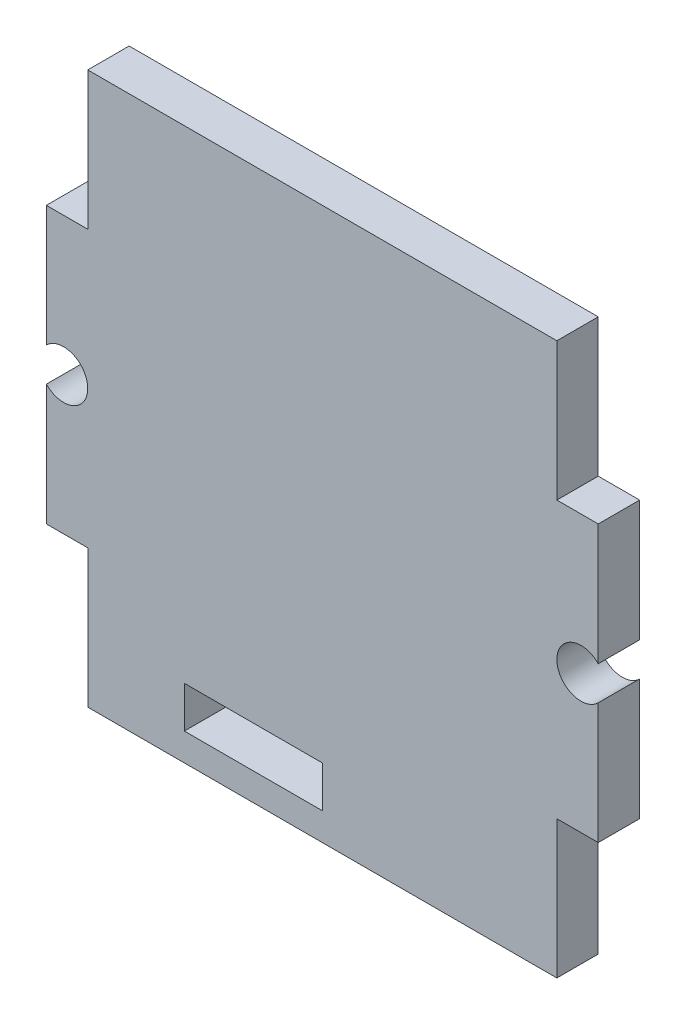
SolidWorks part; units mm, degrees
ref_plane "前视基准面" through (0, 0, 0) normal (0, 0, 1) x (1, 0, 0)
ref_plane "上视基准面" through (0, 0, 0) normal (0, 1, 0) x (1, 0, 0)
ref_plane "右视基准面" through (0, 0, 0) normal (1, 0, 0) x (0, 0, -1)
sketch "草图1" plane through (0, 0, 0) normal (0, 0, 1) x (1, 0, 0)
  line L0 (55, 0) -> (-55, 0) construction
  line L1 (-17, 20) -> (17, 20)
  line L2 (-20, 10) -> (-20, 1.2247)
  line L3 (-17, -20) -> (17, -20)
  line L4 (20, 10) -> (20, 1.2247)
  line L5 (0, -55) -> (0, 55) construction
  line L6 (-17, 20) -> (-17, 10)
  line L7 (-17, 10) -> (-20, 10)
  line L8 (0, 27.5812) -> (0, -27.885) construction
  line L9 (-29.0763, 0) -> (-20.5, 0) construction
  line L10 (17, 10) -> (20, 10)
  line L11 (17, 20) -> (17, 10)
  line L12 (17, -10) -> (20, -10)
  line L13 (17, -20) -> (17, -10)
  line L14 (-17, -10) -> (-20, -10)
  line L15 (-17, -20) -> (-17, -10)
  line L16 (-17, 0) -> (36.3636, 0) construction
  line L17 (-20, -1.2247) -> (-20, -10)
  line L18 (20, -1.2247) -> (20, -10)
  line L20 (-10, -15) -> (0, -15)
  line L21 (-10, -15) -> (-10, -18)
  line L22 (-10, -18) -> (0, -18)
  line L23 (0, -15) -> (0, -18)
  arc A0 (-20, -1.2247) -> (-20, 1.2247) centre (-18.75, 0) ccw
  arc A1 (20, -1.2247) -> (20, 1.2247) centre (18.75, 0) cw
  dimension "D1" = 1.75
  dimension "D2" = 3.5
  dimension "D3" = 20
  dimension "D4" = 20
  dimension "D5" = 3
  dimension "D6" = 10
  dimension "D7" = 3
  dimension "D8" = 2
  dimension "D9" = 10
extrude "凸台-拉伸1" add sketch "草图1" along normal mid plane 3
